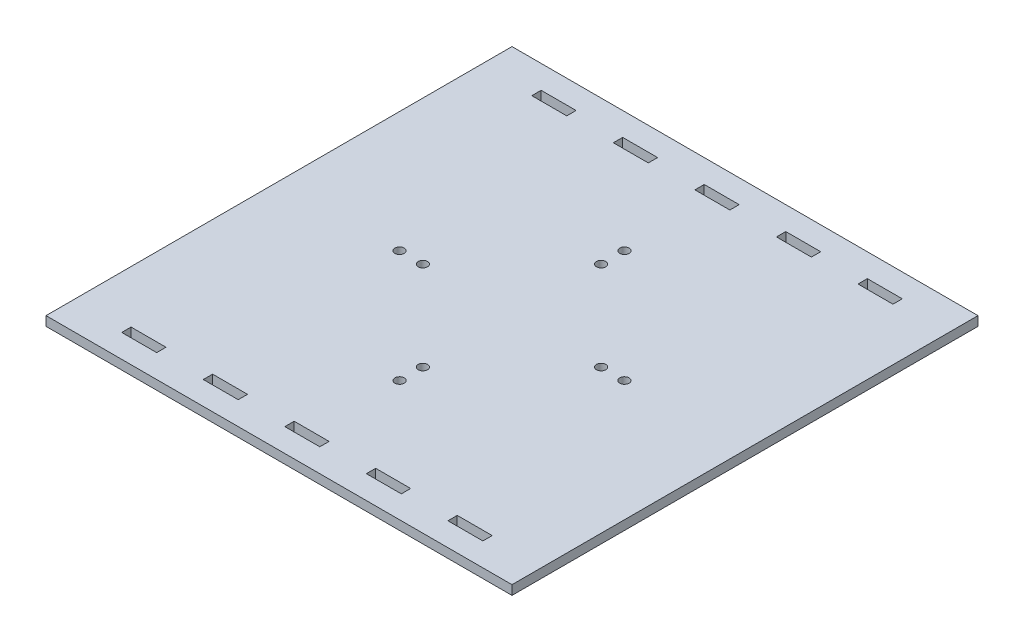
SolidWorks part; units mm, degrees
material "1060 Alloy"
ref_plane "Front Plane" through (0, 0, 0) normal (0, 0, 1) x (1, 0, 0)
ref_plane "Top Plane" through (0, 0, 0) normal (0, 1, 0) x (1, 0, 0)
ref_plane "Right Plane" through (0, 0, 0) normal (1, 0, 0) x (0, 0, -1)
sketch "Sketch1" plane through (0, 0, 0) normal (0, 1, 0) x (1, 0, 0)
  line L0 (0, -100) -> (200, -100) construction
  line L1 (0, 0) -> (200, 0)
  line L2 (0, 0) -> (0, -200)
  line L3 (0, -200) -> (200, -200)
  line L4 (200, 0) -> (200, -200)
  line L5 (22.5, -10) -> (37.5, -10)
  line L6 (22.5, -10) -> (22.5, -14)
  line L7 (22.5, -14) -> (37.5, -14)
  line L8 (37.5, -10) -> (37.5, -14)
  line L9 (57.5, -10) -> (72.5, -10)
  line L10 (57.5, -10) -> (57.5, -14)
  line L11 (57.5, -14) -> (72.5, -14)
  line L12 (72.5, -10) -> (72.5, -14)
  line L13 (92.5, -10) -> (107.5, -10)
  line L14 (92.5, -10) -> (92.5, -14)
  line L15 (92.5, -14) -> (107.5, -14)
  line L16 (107.5, -10) -> (107.5, -14)
  line L17 (127.5, -10) -> (142.5, -10)
  line L18 (127.5, -10) -> (127.5, -14)
  line L19 (127.5, -14) -> (142.5, -14)
  line L20 (142.5, -10) -> (142.5, -14)
  line L21 (162.5, -10) -> (177.5, -10)
  line L22 (162.5, -10) -> (162.5, -14)
  line L23 (162.5, -14) -> (177.5, -14)
  line L24 (177.5, -10) -> (177.5, -14)
  line L25 (177.5, -190) -> (177.5, -186)
  line L26 (162.5, -186) -> (177.5, -186)
  line L27 (162.5, -190) -> (162.5, -186)
  line L28 (162.5, -190) -> (177.5, -190)
  line L29 (142.5, -190) -> (142.5, -186)
  line L30 (127.5, -186) -> (142.5, -186)
  line L31 (127.5, -190) -> (127.5, -186)
  line L32 (127.5, -190) -> (142.5, -190)
  line L33 (107.5, -190) -> (107.5, -186)
  line L34 (92.5, -186) -> (107.5, -186)
  line L35 (92.5, -190) -> (92.5, -186)
  line L36 (92.5, -190) -> (107.5, -190)
  line L37 (72.5, -190) -> (72.5, -186)
  line L38 (57.5, -186) -> (72.5, -186)
  line L39 (57.5, -190) -> (57.5, -186)
  line L40 (57.5, -190) -> (72.5, -190)
  line L41 (37.5, -190) -> (37.5, -186)
  line L42 (22.5, -186) -> (37.5, -186)
  line L43 (22.5, -190) -> (22.5, -186)
  line L44 (22.5, -190) -> (37.5, -190)
  line L45 (100, -71.75) -> (100, -128.25) construction
  line L46 (71.75, -128.25) -> (128.25, -128.25) construction
  line L47 (71.75, -128.25) -> (71.75, -71.75) construction
  line L48 (71.75, -71.75) -> (128.25, -71.75) construction
  line L49 (128.25, -128.25) -> (128.25, -71.75) construction
  line L50 (71.75, -128.25) -> (128.25, -71.75) construction
  line L51 (71.75, -71.75) -> (128.25, -128.25) construction
  circle A0 centre (100, -61.75) radius 2
  circle A1 centre (100, -51.75) radius 2
  circle A2 centre (100, -148.25) radius 2
  circle A3 centre (100, -138.25) radius 2
  circle A4 centre (61.75, -100) radius 2
  circle A5 centre (51.75, -100) radius 2
  circle A6 centre (138.25, -100) radius 2
  circle A7 centre (148.25, -100) radius 2
  point P47 (30, -10)
  point P48 (100, -100)
  point P57 (100, -71.75)
  dimension "D20" = 10
  dimension "D22" = 10
  dimension "D1" = 200
  dimension "D2" = 200
  dimension "D3" = 15
  dimension "D4" = 4
  dimension "D5" = 4
  dimension "D6" = 4
  dimension "D7" = 4
  dimension "D8" = 4
  dimension "D9" = 15
  dimension "D10" = 15
  dimension "D11" = 15
  dimension "D12" = 15
  dimension "D13" = 22.5
  dimension "D14" = 22.5
  dimension "D15" = 20
  dimension "D16" = 20
  dimension "D17" = 20
  dimension "D18" = 20
  dimension "D19" = 10
  dimension "D21" = 10
  dimension "D23" = 10
  dimension "D24" = 56.5
  dimension "D25" = 56.5
extrude "Boss-Extrude1" add sketch "Sketch1" along normal blind 4
